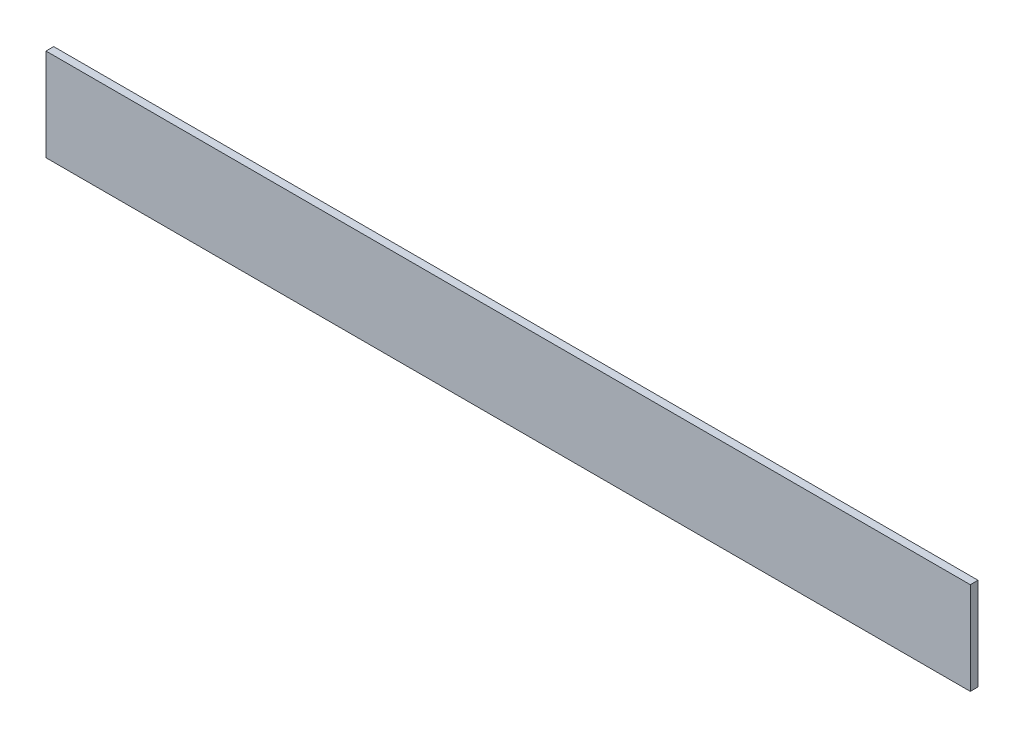
SolidWorks part; units mm, degrees
material "PVC 0.007 Plasticized"
ref_plane "Front Plane" through (0, 0, 0) normal (0, 0, 1) x (1, 0, 0)
ref_plane "Top Plane" through (0, 0, 0) normal (0, 1, 0) x (1, 0, 0)
ref_plane "Right Plane" through (0, 0, 0) normal (1, 0, 0) x (0, 0, -1)
sketch "Sketch1" plane through (0, 0, 0) normal (1, 0, 0) x (0, 0, -1)
  line L1 (-3.175, -38.1) -> (3.175, -38.1)
  line L2 (-3.175, -38.1) -> (-3.175, 38.1)
  line L3 (-3.175, 38.1) -> (3.175, 38.1)
  line L4 (3.175, -38.1) -> (3.175, 38.1)
  line L5 (-3.175, -38.1) -> (3.175, 38.1) construction
  line L6 (-3.175, 38.1) -> (3.175, -38.1) construction
  point P0 (0, 0)
  dimension "D1" = 76.2
  dimension "D2" = 6.35
extrude "Boss-Extrude1" add sketch "Sketch1" along normal blind 762
equation "\"D2@Sketch1\"=1in/4"
